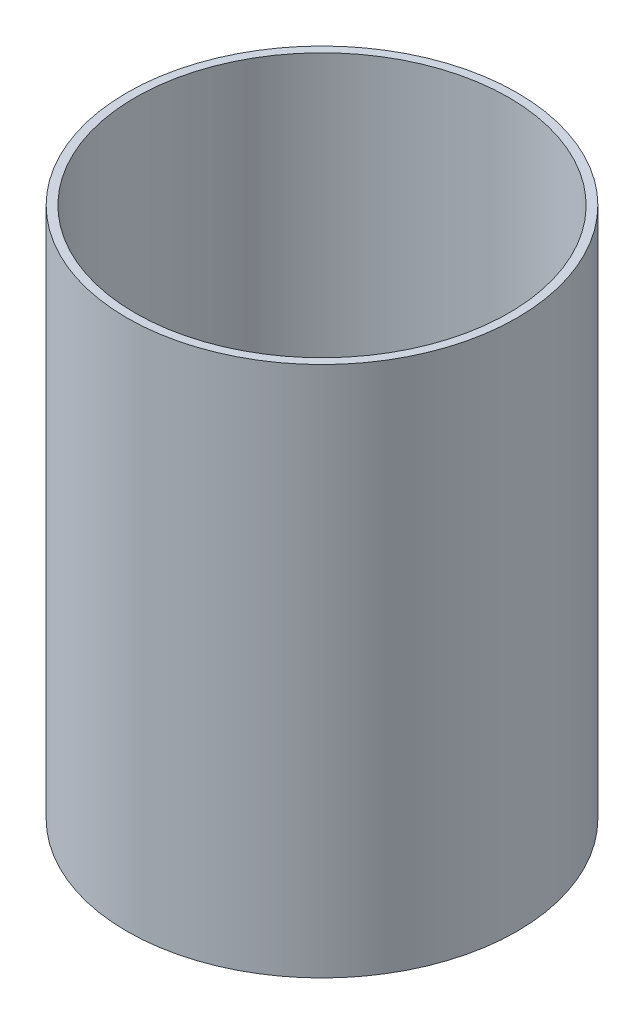
SolidWorks part; units mm, degrees
ref_plane "Front Plane" through (0, 0, 0) normal (0, 0, 1) x (1, 0, 0)
ref_plane "Top Plane" through (0, 0, 0) normal (0, 1, 0) x (1, 0, 0)
ref_plane "Right Plane" through (0, 0, 0) normal (1, 0, 0) x (0, 0, -1)
sketch "Sketch1" plane through (0, 0, 0) normal (0, 1, 0) x (1, 0, 0)
  circle A0 centre (0, 0) radius 142.875
  circle A1 centre (0, 0) radius 149.225
  dimension "D1" = 285.75
  dimension "D2" = 298.45
extrude "Boss-Extrude1" add sketch "Sketch1" along normal blind 406.4
